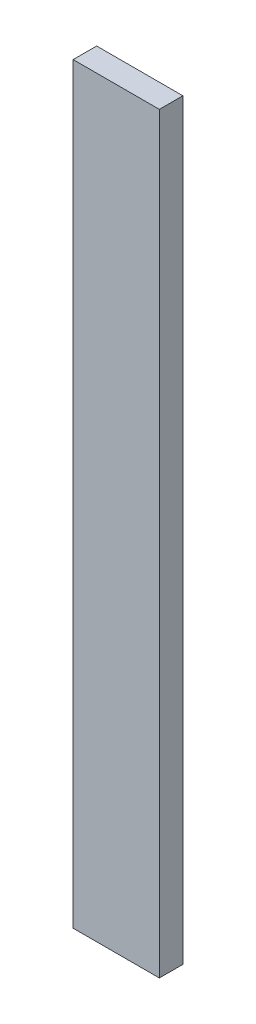
SolidWorks part; units mm, degrees
material "Oak"
ref_plane "Front Plane" through (0, 0, 0) normal (0, 0, 1) x (1, 0, 0)
ref_plane "Top Plane" through (0, 0, 0) normal (0, 1, 0) x (1, 0, 0)
ref_plane "Right Plane" through (0, 0, 0) normal (1, 0, 0) x (0, 0, -1)
sketch "Sketch1" plane through (0, 0, 0) normal (0, 1, 0) x (1, 0, 0)
  line L1 (-69.85, -19.05) -> (69.85, -19.05)
  line L2 (-69.85, -19.05) -> (-69.85, 19.05)
  line L3 (-69.85, 19.05) -> (69.85, 19.05)
  line L4 (69.85, -19.05) -> (69.85, 19.05)
  line L5 (-69.85, -19.05) -> (69.85, 19.05) construction
  line L6 (-69.85, 19.05) -> (69.85, -19.05) construction
  point P0 (0, 0)
  dimension "D1" = 38.1
  dimension "D2" = 139.7
extrude "Boss-Extrude1" add sketch "Sketch1" along normal blind 1219.2 contours L3 L4 L1 L2
